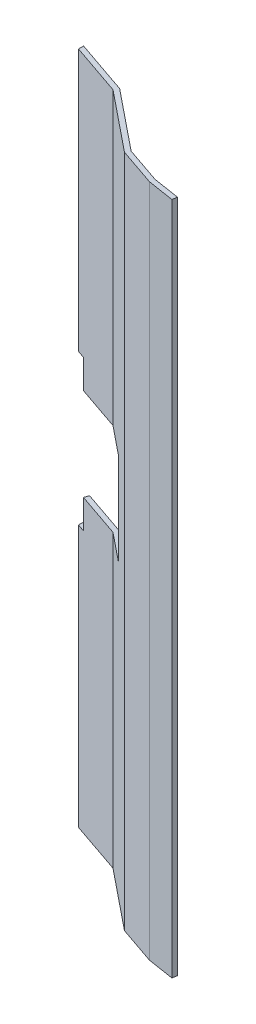
SolidWorks part; units mm, degrees
material "Alum Plate"
ref_plane "Front Plane" through (0, 0, 0) normal (0, 0, 1) x (1, 0, 0)
ref_plane "Top Plane" through (0, 0, 0) normal (0, 1, 0) x (1, 0, 0)
ref_plane "Right Plane" through (0, 0, 0) normal (1, 0, 0) x (0, 0, -1)
sketch "Sketch1" plane through (0, 0, 0) normal (0, 1, 0) x (1, 0, 0)
  line B0 (-37.0626, 23.5832) -> (-37.0626, 21.9048)
  line B1 (-18.9754, 17.3756) -> (-37.0626, 23.5832)
  line B2 (21.3237, -5.6863) -> (21.5743, -4.0939)
  line B3 (12.7923, -2.712) -> (21.5743, -4.0939)
  line B4 (-18.9754, 17.3756) -> (0.7801, 1.4107)
  line B5 (0.7801, 1.4107) -> (12.7923, -2.712)
  line B6 (21.3237, -5.6863) -> (12.5417, -4.3044)
  line B7 (12.5417, -4.3044) -> (0, 0)
  line B8 (0, 0) -> (-19.7555, 15.9649)
  line B9 (-19.7555, 15.9649) -> (-37.0626, 21.9048)
  line B10 (-37.0626, 21.9048) -> (-37.0626, 23.5832)
sketch_block_instance "Wedge sketch block-1"
sketch_block "Wedge sketch block" parameters "D1"=160, "D2"=25.4, "D3"=170, "D4"=1.5875, "D5"=1.5875, "D6"=1.5875, "D7"=160, "D8"=8.89, "D9"=8.89, "D10"=12.7
sketch "Sketch3" plane through (0, 0, 0) normal (0, 1, 0) x (1, 0, 0)
  line L0 (-37.0626, 21.9048) -> (-19.7555, 15.9649)
  line L1 (-19.7555, 15.9649) -> (0, 0)
  line L2 (0, 0) -> (12.5417, -4.3044)
  line L3 (12.5417, -4.3044) -> (21.3237, -5.6863)
  line L4 (21.3237, -5.6863) -> (21.5743, -4.0939)
  line L5 (21.5743, -4.0939) -> (12.7923, -2.712)
  line L6 (12.7923, -2.712) -> (0.7801, 1.4107)
  line L7 (0.7801, 1.4107) -> (-18.9754, 17.3756)
  line L8 (-18.9754, 17.3756) -> (-37.0626, 23.5832)
  line L9 (-37.0626, 23.5832) -> (-37.0626, 21.9048)
  dimension "D1" = 160
  dimension "D2" = 25.4
  dimension "D3" = 1.5875
  dimension "D4" = 1.5875
  dimension "D5" = 19.1227
extrude "Boss-Extrude2" add sketch "Sketch3" along normal blind 222.25
sketch "Sketch4" plane through (3.3354, 0, -9.7184) normal (0.3246, 0, -0.9458) x (-0.9458, 0, -0.3246)
  line L0 (42.711, 222.25) -> (42.711, 0) construction
  line L1 (42.711, 126.365) -> (12.231, 126.365)
  line L2 (42.711, 126.365) -> (42.711, 95.885)
  line L3 (42.711, 95.885) -> (12.231, 95.885)
  line L4 (12.231, 126.365) -> (12.231, 95.885)
  line L6 (-0.2799, 222.25) -> (23.5883, 222.25) construction
  line L7 (23.5883, 0) -> (42.711, 0) construction
  line L9 (42.711, 126.365) -> (39.536, 126.365)
  line L10 (42.711, 126.365) -> (42.711, 135.89)
  line L11 (42.711, 135.89) -> (39.536, 135.89)
  line L12 (39.536, 126.365) -> (39.536, 135.89)
  line L13 (42.711, 95.885) -> (39.536, 95.885)
  line L14 (42.711, 95.885) -> (42.711, 86.36)
  line L15 (42.711, 86.36) -> (39.536, 86.36)
  line L16 (39.536, 95.885) -> (39.536, 86.36)
  line M6 (42.711, 0) -> (42.711, 222.25)
  line M8 (23.5883, 222.25) -> (23.5883, 0)
  dimension "D1" = 95.885
  dimension "D2" = 95.885
  dimension "D3" = 30.48
  dimension "D4" = 3.175
  dimension "D5" = 3.175
  dimension "D6" = 9.525
  dimension "D7" = 9.525
extrude "Cut-Extrude2" cut sketch "Sketch4" against normal through all both and the other way through all contours L12 L1 L11 M6 | L3 L1 M6 M8 | L3 L16 L15 M6 | L1 L4 L3 M8
